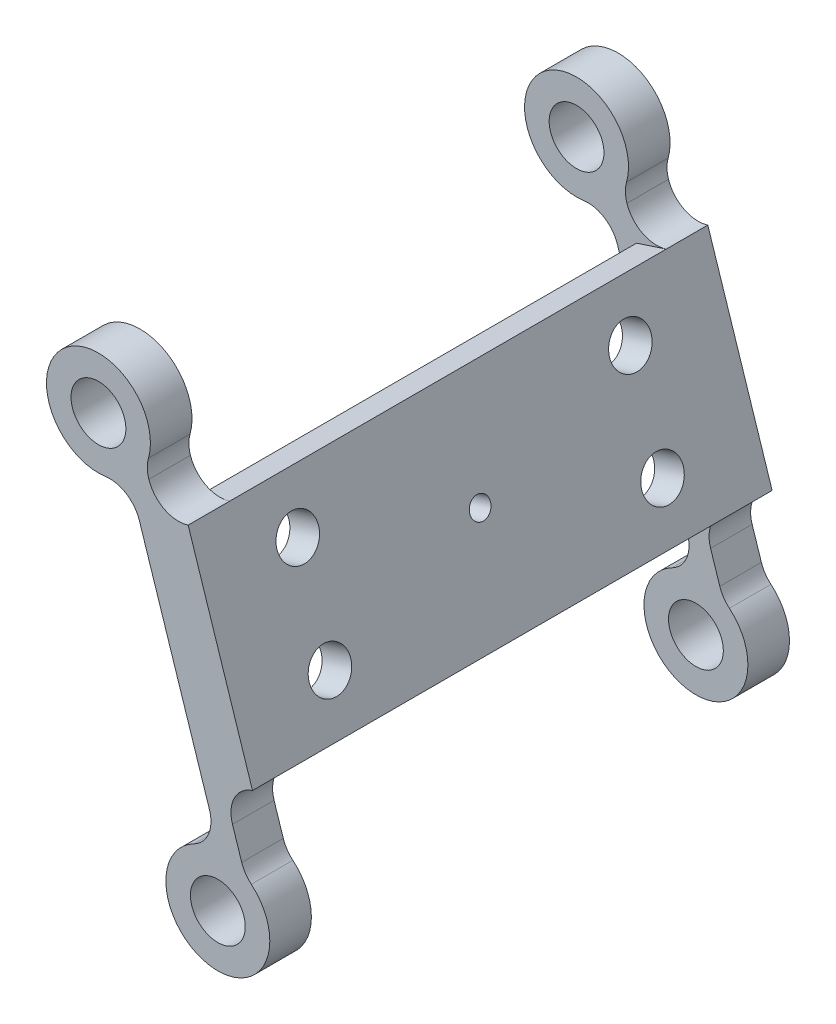
SolidWorks part; units mm, degrees
material "PLA"
ref_plane "Front Plane" through (0, 0, 0) normal (0, 0, 1) x (1, 0, 0)
ref_plane "Top Plane" through (0, 0, 0) normal (0, 1, 0) x (1, 0, 0)
ref_plane "Right Plane" through (0, 0, 0) normal (1, 0, 0) x (0, 0, -1)
ref_plane "Plane1" through (-8.3424, 25.6288, 0) normal (0.3095, -0.9509, 0) x (0.9509, 0.3095, 0)
sketch "Sketch1" plane through (-8.3424, 25.6288, 0) normal (0.3095, -0.9509, 0) x (0.9509, 0.3095, 0)
  line L0 (-4.1403, -30.713) -> (-4.1403, -23.5892)
  arc A0 (-5.8855, -25.4852) -> (-5.8855, -29.4852) centre (-5.8855, -27.4852) ccw
  spline S0 degree 3 poles (-4.1403, -23.5892) (-4.2208, -24.2795) (-4.8025, -24.9115) (-5.8855, -25.4852) knots 0 0 0 0 1 1 1 1
  spline S1 degree 3 poles (-5.8855, -29.4852) (-4.9844, -29.7286) (-4.4027, -30.1379) (-4.1403, -30.713) knots 0 0 0 0 1 1 1 1
extrude "Boss-Extrude1" add sketch "Sketch1" against normal blind 5
ref_plane "Plane2" through (-3.937, -1.2815, 0) normal (-0.9509, -0.3095, 0) x (0, 0, 1)
sketch "Sketch6" plane through (-3.937, -1.2815, 0) normal (-0.9509, -0.3095, 0) x (0, 0, 1)
  line L0 (0, 39.4524) -> (-42, 39.4524)
  line L1 (-42, 39.4524) -> (-42, 19.4524)
  line L2 (-42, 19.4524) -> (0, 19.4524)
  line L3 (0, 19.4524) -> (0, 39.4524)
extrude "Boss-Extrude2" add sketch "Sketch6" against normal blind 3
sketch "Sketch8" plane through (0, 0, 0) normal (0, 0, 1) x (1, 0, 0)
  line L0 (-17.3976, 40.0711) -> (-17.077, 39.0861)
  line L1 (-13.2958, 37.162) -> (-7.1053, 18.1442)
  line L2 (-9.0294, 14.3629) -> (-7.8424, 10.7162)
  line L3 (-10.2569, 11.44) -> (-18.9568, 38.1671)
  arc A0 (-17.077, 39.0861) -> (-13.2958, 37.162) centre (-14.2243, 40.0147) ccw
  arc A1 (-7.1053, 18.1442) -> (-9.0294, 14.3629) centre (-6.1767, 15.2915) ccw
  arc A2 (-7.8424, 10.7162) -> (-10.2569, 11.44) centre (-10.4388, 6.4433) cw
  arc A3 (-18.9568, 38.1671) -> (-17.3976, 40.0711) centre (-21.9266, 42.1896) cw
extrude "Boss-Extrude3" add sketch "Sketch8" along normal blind 4
ref_plane "Plane3" through (-6.021, 18.4971, 0) normal (0.3095, -0.9509, 0) x (-0.9509, -0.3095, 0)
sketch "Sketch14" plane through (-6.021, 18.4971, 0) normal (0.3095, -0.9509, 0) x (-0.9509, -0.3095, 0)
  line L0 (4.1403, 42) -> (4.1403, 0)
  line L1 (4.1403, 0) -> (1.1403, 0)
  line L2 (1.1403, 0) -> (1.1403, 42)
  line L3 (1.1403, 42) -> (4.1403, 42)
extrude "Boss-Extrude4" add sketch "Sketch14" along normal blind 3
sketch "Sketch15" plane through (-5.0924, 15.6444, 0) normal (0.3095, -0.9509, 0) x (0.9509, 0.3095, 0)
  line L0 (-4.1403, 0) -> (-4.1403, -42)
  line L1 (-4.1403, -42) -> (-1.1403, -42)
  line L2 (-1.1403, -42) -> (-1.1403, 0)
  line L3 (-1.1403, 0) -> (-4.1403, 0)
extrude "Cut-Extrude1" cut sketch "Sketch15" against normal blind 3
ref_plane "Plane4" through (0, 0, -42) normal (0, 0, -1) x (-1, 0, 0)
sketch "Sketch22" plane through (0, 0, -42) normal (0, 0, -1) x (-1, 0, 0)
  line L0 (18.9568, 38.1671) -> (10.2569, 11.44)
  line L1 (7.8424, 10.7162) -> (9.0294, 14.3629)
  line L2 (7.1053, 18.1442) -> (13.2958, 37.162)
  line L3 (17.077, 39.0861) -> (17.3976, 40.0711)
  arc A0 (17.3976, 40.0711) -> (18.9568, 38.1671) centre (21.9266, 42.1896) cw
  arc A1 (10.2569, 11.44) -> (7.8424, 10.7162) centre (10.4388, 6.4433) cw
  arc A2 (9.0294, 14.3629) -> (7.1053, 18.1442) centre (6.1767, 15.2915) ccw
  arc A3 (13.2958, 37.162) -> (17.077, 39.0861) centre (14.2243, 40.0147) ccw
extrude "Boss-Extrude5" add sketch "Sketch22" along normal blind 4
hole_wizard "Ø2.0 (2) Diameter Hole1" positions "Sketch24" profile "Sketch23" hole size "Ø2.0" standard "ANSI Metric"
sketch "Sketch24" plane through (-3.937, -1.2815, 0) normal (-0.9509, -0.3095, 0) x (0, 0, 1)
  point P0 (-21, 29.4524)
sketch "Sketch23" plane through (-13.0532, 26.7245, -21) normal (0, 0, 1) x (0.3095, -0.9509, 0)
  line L0 (0, 0) -> (0, 13.5749)
  line L1 (0, 13.5749) -> (1, 13.5749)
  line L2 (1, 13.5749) -> (1, 0)
  line L5 (1, 0) -> (0, 0)
  line L11 (0, -6.35) -> (0, 107.95) construction
  dimension "Thru Hole Dia." = 2
  dimension "Thru Hole Depth" = 13.5749
hole_wizard "Ø4.0 (4) Diameter Hole1" positions "Sketch26" profile "Sketch25" hole size "Ø4.0" standard "ANSI Metric"
sketch "Sketch26" plane through (-3.937, -1.2815, 0) normal (-0.9509, -0.3095, 0) x (0, 0, 1)
  point P0 (-5, 24.4524)
  point P1 (-37, 24.4524)
  point P2 (-37, 34.4524)
  point P3 (-5, 34.4524)
sketch "Sketch25" plane through (-11.5056, 21.9701, -5) normal (0, 0, 1) x (0.3095, -0.9509, 0)
  line L0 (0, 0) -> (0, 13.5749)
  line L1 (0, 13.5749) -> (2, 13.5749)
  line L2 (2, 13.5749) -> (2, 0)
  line L5 (2, 0) -> (0, 0)
  line L11 (0, -6.35) -> (0, 107.95) construction
  dimension "Thru Hole Dia." = 4
  dimension "Thru Hole Depth" = 13.5749
hole_wizard "Hole1" positions "Sketch28" profile "Sketch27" legacy
sketch "Sketch28" plane through (0, 0, -46) normal (0, 0, -1) x (-1, 0, 0)
  point P0 (10.4388, 6.4433)
  point P1 (21.9266, 42.1896)
sketch "Sketch27" plane through (-10.4388, 6.4433, -46) normal (1, 0, 0) x (0, 1, 0)
  line L0 (0, 0) -> (0, 4)
  line L1 (0, 4) -> (2.6375, 4)
  line L2 (2.6375, 4) -> (2.6375, 0)
  line L3 (2.6375, 0) -> (0, 0)
  line L4 (0, 110) -> (0, -10) construction
  dimension "Diameter" = 5.275
  dimension "Depth" = 4
hole_wizard "Hole2" positions "Sketch30" profile "Sketch29" legacy
sketch "Sketch30" plane through (0, 0, 0) normal (0, 0, -1) x (-1, 0, 0)
  point P0 (10.4388, 6.4433)
  point P1 (21.9266, 42.1896)
sketch "Sketch29" plane through (-10.4388, 6.4433, 0) normal (1, 0, 0) x (0, 1, 0)
  line L0 (0, 0) -> (0, 4)
  line L1 (0, 4) -> (2.6375, 4)
  line L2 (2.6375, 4) -> (2.6375, 0)
  line L3 (2.6375, 0) -> (0, 0)
  line L4 (0, 110) -> (0, -10) construction
  dimension "Diameter" = 5.275
  dimension "Depth" = 4
hole_wizard "Ø3.0 (3) Diameter Hole1" positions "Sketch32" profile "Sketch31" hole size "Ø3.0" standard "ANSI Metric"
sketch "Sketch32" plane through (-8.3424, 25.6288, 0) normal (0.3095, -0.9509, 0) x (-0.9509, -0.3095, 0)
  point P0 (5.8855, 27.4852)
sketch "Sketch31" plane through (-13.9389, 23.8071, -27.4852) normal (0, 0, 1) x (0.9509, 0.3095, 0)
  line L0 (0, 0) -> (0, 26.2542)
  line L1 (0, 26.2542) -> (1.5, 26.2542)
  line L2 (1.5, 26.2542) -> (1.5, 0)
  line L5 (1.5, 0) -> (0, 0)
  line L11 (0, -6.35) -> (0, 107.95) construction
  dimension "Thru Hole Dia." = 3
  dimension "Thru Hole Depth" = 26.2542
fillet "Fillet1" radius 3 8 edges at (-17.3976, 40.0711, -44) (-7.8424, 10.7162, -44) (-18.9568, 38.1671, -44) (-17.3976, 40.0711, 2) (-18.9568, 38.1671, 2) (-10.2569, 11.44, 2) (-7.8424, 10.7162, 2) (-10.2569, 11.44, -44)
